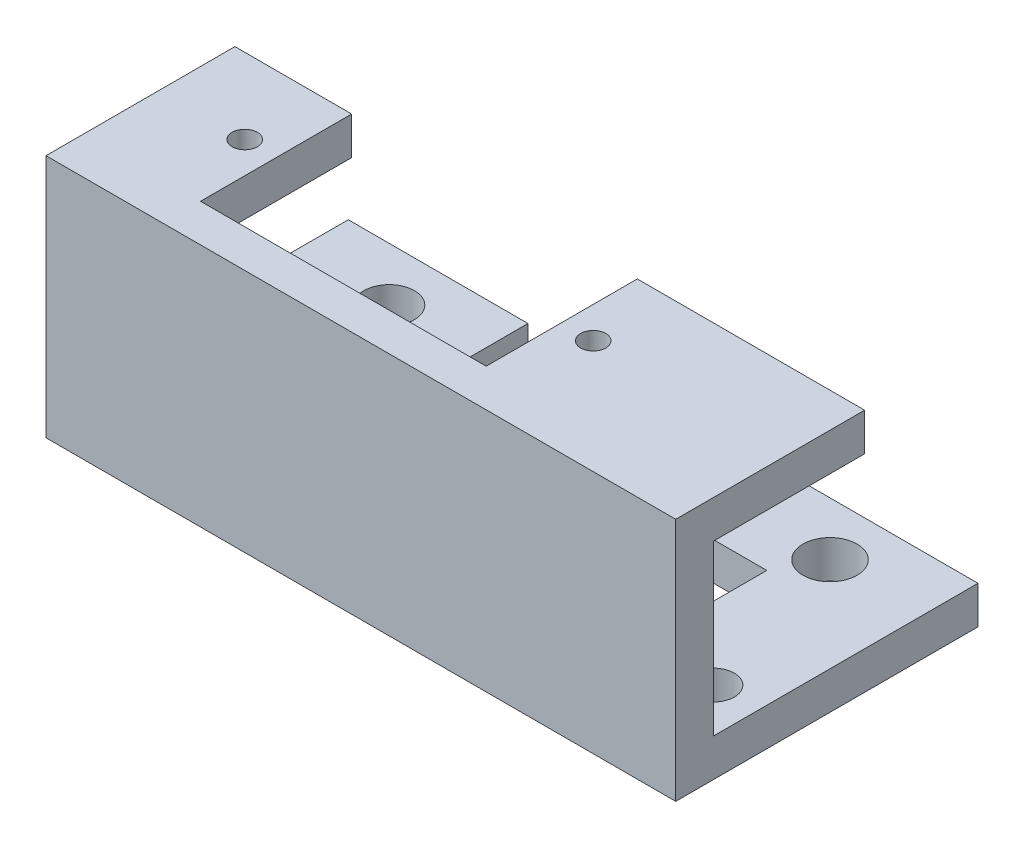
SolidWorks part; units mm, degrees
ref_plane "前视基准面" through (0, 0, 0) normal (0, 0, 1) x (1, 0, 0)
ref_plane "上视基准面" through (0, 0, 0) normal (0, 1, 0) x (1, 0, 0)
ref_plane "右视基准面" through (0, 0, 0) normal (1, 0, 0) x (0, 0, -1)
sketch "草图1" plane through (0, 0, 0) normal (0, 0, 1) x (1, 0, 0)
  line L1 (0, 0) -> (50, 0)
  line L2 (0, 0) -> (0, 19.4)
  line L3 (0, 19.4) -> (50, 19.4)
  line L4 (50, 0) -> (50, 19.4)
extrude "凸台-拉伸1" add sketch "草图1" along normal blind 3
sketch "草图2" plane through (0, 0, 0) normal (0, 0, -1) x (-1, 0, 0)
  line L0 (-50, 19.4) -> (0, 19.4) construction
  line L5 (-25, 19.4) -> (-25, 0)
  line L6 (0, 0) -> (-50, 0) construction
  line L8 (-50, 19.4) -> (-31.95, 19.4)
  line L9 (-50, 19.4) -> (-50, 16.4)
  line L10 (-50, 16.4) -> (-31.95, 16.4)
  line L11 (-31.95, 19.4) -> (-31.95, 16.4)
  line L12 (0, 19.4) -> (-9.27, 19.4)
  line L13 (0, 19.4) -> (0, 16.4)
  line L14 (0, 16.4) -> (-9.27, 16.4)
  line L15 (-9.27, 19.4) -> (-9.27, 16.4)
extrude "凸台-拉伸3" add sketch "草图2" along normal blind 12 contours L9 L8 L11 L10 | L13 L12 L15 L14
sketch "草图5" plane through (0, 19.4, 0) normal (0, 1, 0) x (1, 0, 0)
  line L0 (50, -3) -> (0, -3) construction
  line L1 (25, -3) -> (25, 0)
  line L2 (31.95, 0) -> (9.27, 0) construction
  line L3 (25, 0) -> (34.45, 0)
  line L4 (34.45, 0) -> (34.45, 6)
  line L5 (25, 0) -> (6.78, 0)
  line L6 (6.78, 0) -> (6.78, 6)
  circle A0 centre (34.45, 6) radius 1
  circle A1 centre (6.78, 6) radius 1
extrude "切除-拉伸1" cut sketch "草图5" against normal blind 4
sketch "草图6" plane through (0, 0, 0) normal (0, 0, -1) x (-1, 0, 0)
  line L0 (0, 0) -> (-50, 0) construction
  line L1 (-25, 0) -> (-25, 19.4)
  line L2 (-31.95, 19.4) -> (-9.27, 19.4) construction
  line L3 (-50, 2.9967) -> (-40.73, 2.9967)
  line L4 (0, 0) -> (-9.27, 0)
  line L5 (0, 0) -> (0, 2.9967)
  line L6 (0, 2.9967) -> (-9.27, 2.9967)
  line L7 (-9.27, 0) -> (-9.27, 2.9967)
  line L8 (-40.73, 0) -> (-40.73, 2.9967)
  line L9 (-50, 0) -> (-40.73, 0)
  line L10 (-50, 0) -> (-50, 2.9967)
  line M10 (-50, 16.4) -> (-50, 0)
  line M11 (-50, 0) -> (0, 0)
extrude "凸台-拉伸5" add sketch "草图6" along normal blind 21 contours L8 L3 M11 M10 | L6 L7 L4 L5
sketch "草图9" plane through (9.27, 0, 0) normal (1, 0, 0) x (0, 0, -1)
  line L0 (21, 0) -> (0, 0) construction
  line L1 (21, 2.9967) -> (13.5, 2.9967)
  line L2 (21, 2.9967) -> (21, 0)
  line L3 (21, 0) -> (13.5, 0)
  line L4 (13.5, 2.9967) -> (13.5, 0)
extrude "凸台-拉伸6" add sketch "草图9" along normal blind 5
sketch "草图10" plane through (40.73, 0, 0) normal (-1, 0, 0) x (0, 0, 1)
  line L0 (-21, 0) -> (0, 0) construction
  line L1 (-21, 2.9967) -> (-13.5, 2.9967)
  line L2 (-21, 2.9967) -> (-21, 0)
  line L3 (-21, 0) -> (-13.5, 0)
  line L4 (-13.5, 2.9967) -> (-13.5, 0)
extrude "凸台-拉伸7" add sketch "草图10" along normal blind 5
sketch "草图11" plane through (0, 2.9967, 0) normal (0, 1, 0) x (1, 0, 0)
  line L1 (50, 0) -> (46.5, 0)
  line L2 (50, 0) -> (40.73, 0) construction
  line L3 (35.73, 16.75) -> (42.5, 16.75)
  line L4 (46.5, 0) -> (46.5, 3.5)
  line L5 (35.73, 13.5) -> (35.73, 21) construction
  line L6 (40.73, 0) -> (9.27, 0) construction
  line L7 (25, 0) -> (25, 35.6278) construction
  circle A0 centre (42.5, 16.75) radius 2.15
  circle A1 centre (46.5, 3.5) radius 1.65
  dimension "D1" = 4.3
  dimension "D4" = 3.3
  dimension "D2" = 13.25
  dimension "D3" = 3.5
  dimension "D5" = 17.5
  dimension "D6" = 21.5
extrude "切除-拉伸3" cut sketch "草图11" against normal blind 5
sketch "草图12" plane through (0, 2.9967, 0) normal (0, 1, 0) x (1, 0, 0)
  line L1 (14.27, 16.75) -> (7.5, 16.75)
  line L2 (0, 0) -> (3.5, 0)
  line L3 (0, 0) -> (9.27, 0) construction
  line L4 (3.5, 0) -> (3.5, 3.5)
  circle A0 centre (7.5, 16.75) radius 2
  circle A1 centre (3.5, 3.5) radius 1.65
  dimension "D1" = 3.5
  dimension "D2" = 13.25
extrude "切除-拉伸4" cut sketch "草图12" against normal blind 5
